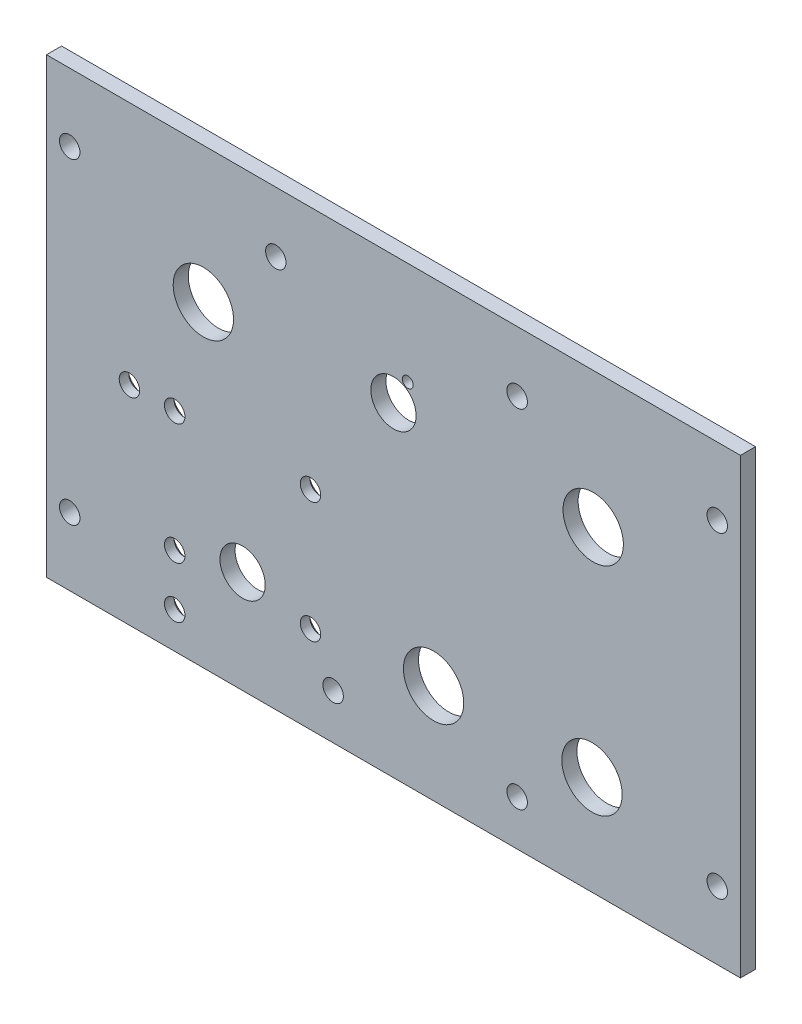
SolidWorks part; units mm, degrees
material "Acrylic (Medium-high impact)"
ref_plane "Front Plane" through (0, 0, 0) normal (0, 0, 1) x (1, 0, 0)
ref_plane "Top Plane" through (0, 0, 0) normal (0, 1, 0) x (1, 0, 0)
ref_plane "Right Plane" through (0, 0, 0) normal (1, 0, 0) x (0, 0, -1)
sketch "Sketch1" plane through (0, 0, 0) normal (0, 0, 1) x (1, 0, 0)
  line L8 (0, 95.25) -> (-146.05, 95.25)
  line L9 (-146.05, 95.25) -> (-146.05, 0)
  line L10 (-146.05, 0) -> (0, 0)
  line L11 (0, 0) -> (0, 95.25)
extrude "Boss-Extrude1" add sketch "Sketch1" against normal blind 3.175
hole_wizard "#6 Clearance Hole1" positions "Sketch3" profile "Sketch2" hole size "#6" standard "ANSI Inch" end condition through all
sketch "Sketch3" plane through (0, 0, -3.175) normal (0, 0, -1) x (-1, 0, 0)
  point P0 (4.8895, 80.9625)
  point P3 (141.1605, 80.9625)
  point P6 (141.1605, 14.2875)
  point P9 (4.8895, 14.2875)
  point P12 (46.99, 9.525)
  point P15 (85.725, 9.525)
  point P18 (97.79, 82.55)
  point P21 (46.99, 82.55)
sketch "Sketch2" plane through (-4.8895, 80.9625, -3.175) normal (1, 0, 0) x (0, 1, 0)
  line L0 (0, 0) -> (0, 3.175)
  line L1 (0, 3.175) -> (2.1526, 3.175)
  line L2 (2.1526, 3.175) -> (2.1526, 0)
  line L5 (2.1526, 0) -> (0, 0)
  line L11 (0, -6.35) -> (0, 107.95) construction
  dimension "Thru Hole Dia." = 4.3053
  dimension "Thru Hole Depth" = 3.175
sketch "Sketch5" plane through (0, 0, -7.4676) normal (0, 0, -1) x (-1, 0, 0)
  circle A0 centre (30.988, 66.675) radius 6.35
  circle A1 centre (113.03, 66.675) radius 6.35
  circle A2 centre (64.5795, 20.955) radius 6.35
  circle A3 centre (31.242, 20.955) radius 6.35
  circle A4 centre (73.025, 68.326) radius 4.7625
  circle A5 centre (104.775, 21.59) radius 4.7625
  dimension "D1" = 12.7
  dimension "D2" = 9.525
extrude "Cut-Extrude1" cut sketch "Sketch5" against normal through all
hole_wizard "CSK for #6 Flat Head Machine Screw (100)1" positions "Sketch7" profile "Sketch6" countersink size "#6" standard "ANSI Inch" end condition through all
sketch "Sketch7" plane through (0, 0, -3.175) normal (0, 0, -1) x (-1, 0, 0)
  point P0 (90.4875, 43.815)
  point P3 (90.4875, 18.415)
  point P6 (119.0625, 7.6362)
  point P9 (119.0625, 18.415)
  point P12 (119.0625, 43.815)
  point P15 (128.5875, 43.815)
sketch "Sketch6" plane through (-90.4875, 43.815, -3.175) normal (1, 0, 0) x (0, 1, 0)
  line L0 (0, 0) -> (0, 3.175)
  line L1 (0, 3.175) -> (2.1526, 3.175)
  line L2 (2.1526, 3.175) -> (2.1526, 1.1669)
  line L3 (2.1526, 1.1669) -> (3.5433, 0)
  line L5 (3.5433, 0) -> (0, 0)
  line L6 (-2.1526, 1.1669) -> (-3.5433, 0) construction
  line L11 (0, -6.35) -> (0, 107.95) construction
  dimension "Thru Hole Dia." = 4.3053
  dimension "Thru Hole Depth" = 3.175
  dimension "Near C'Sink Dia." = 7.0866
  dimension "Near C'Sink Angle" = 100
sketch "Sketch8" plane through (0, 0, 0) normal (0, 0, 1) x (1, 0, 0)
  circle A0 centre (-70.0124, 73.6066) radius 1.1345
  point P2 (-68.021, 66.1144)
  point P3 (-70.5349, 73.4423)
  point P4 (-70.7874, 74.0293)
  point P5 (-69.9067, 73.5538)
  point P6 (-70.0124, 73.6066)
extrude "Cut-Extrude2" cut sketch "Sketch8" against normal through all
